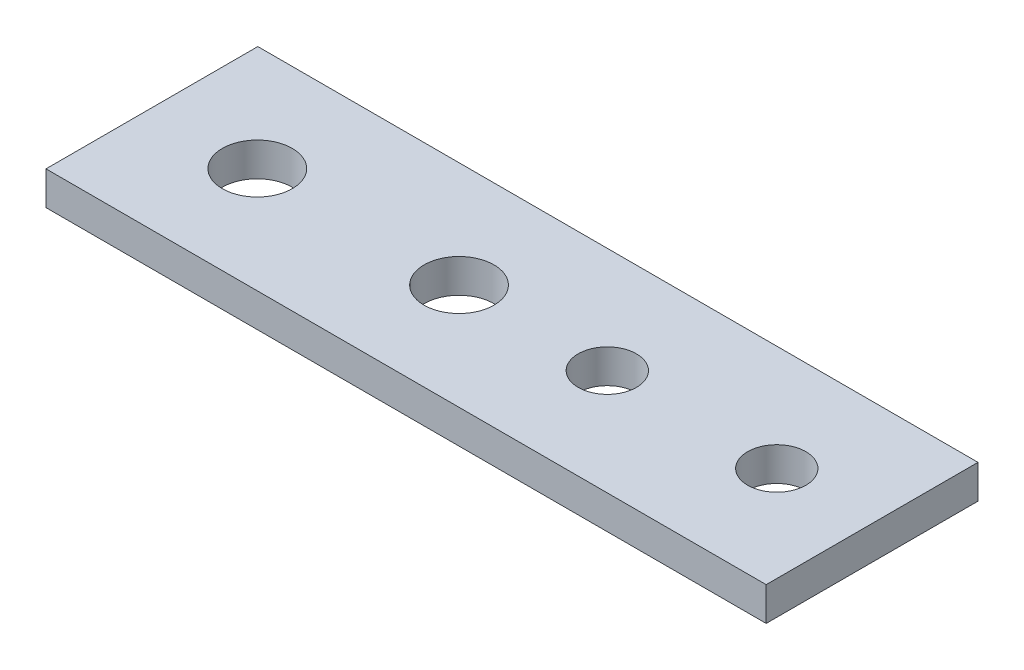
SolidWorks part; units mm, degrees
ref_plane "Front Plane" through (0, 0, 0) normal (0, 0, 1) x (1, 0, 0)
ref_plane "Top Plane" through (0, 0, 0) normal (0, 1, 0) x (1, 0, 0)
ref_plane "Right Plane" through (0, 0, 0) normal (1, 0, 0) x (0, 0, -1)
sketch "Sketch1" plane through (0, 0, 0) normal (0, 1, 0) x (1, 0, 0)
  line L1 (0, 0) -> (-68, 0)
  line L2 (0, 0) -> (0, 20)
  line L3 (0, 20) -> (-68, 20)
  line L4 (-68, 0) -> (-68, 20)
  dimension "D1" = 20
  dimension "D2" = 68
extrude "Boss-Extrude1" add sketch "Sketch1" along normal blind 3.175
sketch "Sketch2" plane through (0, 3.175, 0) normal (0, 1, 0) x (1, 0, 0)
  line L0 (-34, 20) -> (-34, 0) construction
  line L1 (0, 20) -> (-68, 20) construction
  line L2 (-68, 0) -> (0, 0) construction
  line L3 (-68, 10) -> (0, 10) construction
  line L4 (-68, 20) -> (-68, 0) construction
  line L5 (0, 0) -> (0, 20) construction
  point P12 (-58.05, 10)
  point P13 (-39, 10)
  dimension "D1" = 5
  dimension "19" = 19.05
hole_wizard "M6 Clearance Hole1" positions "3DSketch1" profile "Sketch3" hole size "M6" standard "ANSI Metric"
sketch3d "3DSketch1"
  point P0 (-39, 3.175, -10)
  point P3 (-58.05, 3.175, -10)
sketch "Sketch3" plane through (-39, 3.175, -10) normal (1, 0, 0) x (0, 0, 1)
  line L0 (0, 0) -> (0, 15.9828)
  line L1 (0, 15.9828) -> (3.3, 14)
  line L2 (3.3, 14) -> (3.3, 0)
  line L5 (3.3, 0) -> (0, 0)
  line L10 (0, 15.9828) -> (-3.3, 14) construction
  line L11 (0, -6.35) -> (0, 107.95) construction
  dimension "Hole Dia." = 6.6
  dimension "Hole Depth" = 14
  dimension "Drill Angle" = 118
sketch "Sketch4" plane through (0, 3.175, 0) normal (0, 1, 0) x (1, 0, 0)
  line L0 (-34, 10) -> (0, 10) construction
  line L1 (-34, 20) -> (-34, 0) construction
  line L2 (-17, 0) -> (-17, 20) construction
  line L3 (0, 20) -> (-68, 20) construction
  point P5 (-25, 10)
  point P10 (-17, 10)
  point P11 (-9, 10)
  dimension "D1" = 8
hole_wizard "M5 Clearance Hole1" positions "3DSketch2" profile "Sketch5" hole size "M5" standard "ANSI Metric"
sketch3d "3DSketch2"
  point P0 (-25, 3.175, -10)
  point P3 (-9, 3.175, -10)
sketch "Sketch5" plane through (-25, 3.175, -10) normal (1, 0, 0) x (0, 0, 1)
  line L0 (0, 0) -> (0, 15.6524)
  line L1 (0, 15.6524) -> (2.75, 14)
  line L2 (2.75, 14) -> (2.75, 0)
  line L5 (2.75, 0) -> (0, 0)
  line L10 (0, 15.6524) -> (-2.75, 14) construction
  line L11 (0, -6.35) -> (0, 107.95) construction
  dimension "Hole Dia." = 5.5
  dimension "Hole Depth" = 14
  dimension "Drill Angle" = 118
